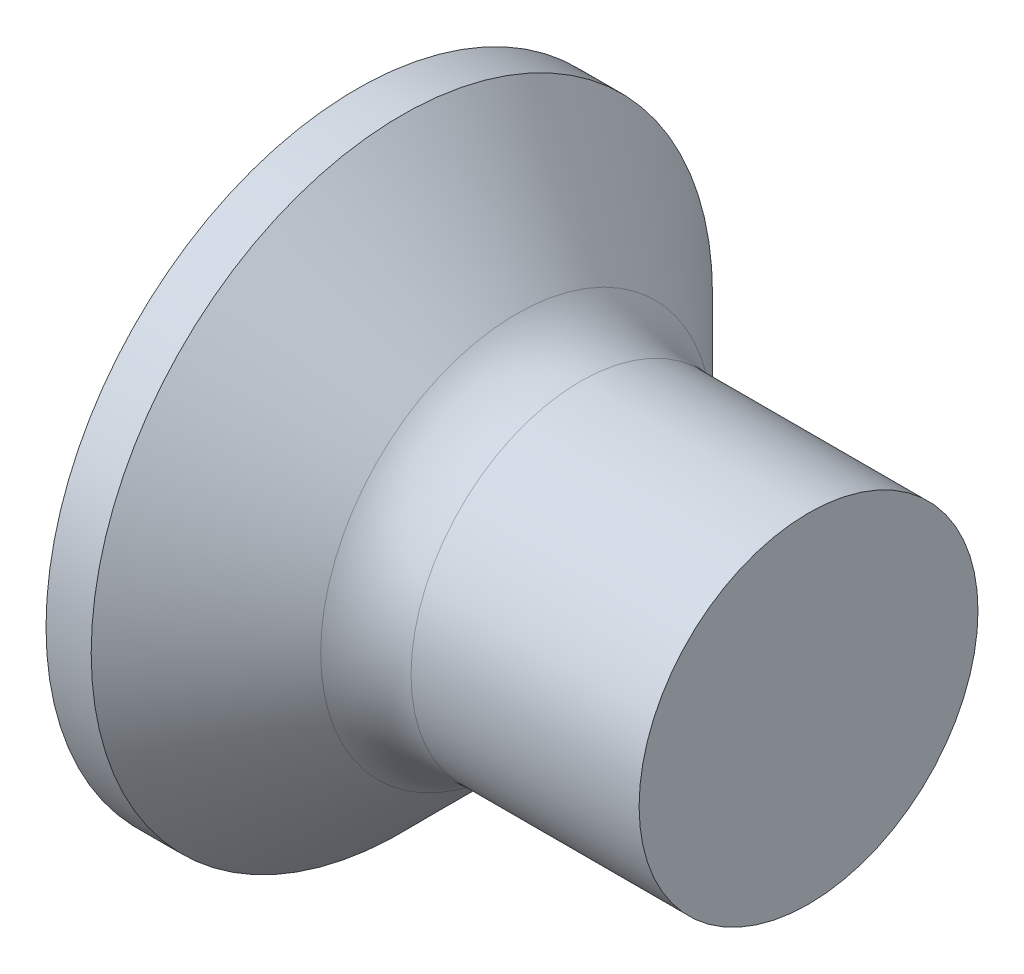
SolidWorks part; units mm, degrees
revolve "Base-Revolve" add sketch "BodySke"
sketch "BodySke" plane through (0, 0, 0) normal (0, 0, 1) x (1, 0, 0)
  line L0 (0, 0) -> (0, 2.75)
  line L1 (0, 2.75) -> (0.4, 2.75)
  line L2 (1.65, 1.5) -> (4, 1.5)
  line L3 (4, 1.5) -> (4, 0)
  line L4 (4, 0) -> (0, 0)
  line L5 (-6.35, 0) -> (82.55, 0) construction
  line L6 (1.65, -1.5) -> (4, -1.5) construction
  line L7 (0.4, -2.75) -> (1.65, -1.5) construction
  line L8 (0.4, 2.75) -> (1.65, 1.5)
  line L9 (0, -2.75) -> (0.4, -2.75) construction
  line L10 (2.15, 3.0875) -> (2.15, -6.4375) construction
  line L11 (0, 6.35) -> (0, -3.175) construction
  dimension "Diameter" = 3
  dimension "Length" = 4
  dimension "Head_ht" = 1.65
  dimension "Head_dia" = 5.5
  dimension "Head_ang" = 90
  dimension "D6" = 0.4
  dimension "Advance" = 0.5
  dimension "Thread_nom" = 4
cosmetic thread "ThreadCosmetic" [suppressed]
fillet "Fillet1" radius 0.8 1 edges at (1.65, 0, 1.5)
ref_plane "Plane1" through (0, 0, 0) normal (0, 0, 1) x (1, 0, 0)
ref_plane "Plane2" through (0, 0, 0) normal (0, 1, 0) x (1, 0, 0)
ref_plane "Plane3" through (0, 0, 0) normal (1, 0, 0) x (0, 0, -1)
sketch "Sketch3" plane through (0, 0, 0) normal (-1, 0, 0) x (0, 0, 1)
  line L0 (-0.37, 1.5) -> (0.37, 1.5)
  line L1 (0.37, 1.5) -> (0.37, -1.5)
  line L2 (0.37, -1.5) -> (-0.37, -1.5)
  line L3 (-0.37, -1.5) -> (-0.37, 1.5)
  dimension "Cross_dia" = 3
  dimension "Cross_width" = 0.74
  dimension "D1" = 1.5
  dimension "D2" = 0.37
ref_plane "Plane4" through (2.01, 0, 0) normal (-1, 0, 0) x (0, 0, 1)
sketch "Sketch4" plane through (2.01, 0, 0) normal (-1, 0, 0) x (0, 0, 1)
  line L0 (-0.37, 0.4979) -> (0.37, 0.4979)
  line L3 (0.37, 0.4979) -> (0.37, -0.4979)
  line L4 (0.37, -0.4979) -> (-0.37, -0.4979)
  line L5 (-0.37, -0.4979) -> (-0.37, 0.4979)
  dimension "D2" = 0.9957
  dimension "D1" = 0.74
  dimension "D4" = 0.4979
  dimension "D3" = 0.37
loft "Recess" cut profiles "Sketch3", "Sketch4"
pattern_circular "RecPat" count 2 every 90 about axis through (0, 0, 0) along (1, 0, 0) of "Recess"
sketch "RecCorSke" plane through (0, 0, 0) normal (0, 0, 1) x (1, 0, 0)
  line L0 (-3.175, 0) -> (15.875, 0) construction
  line L2 (0, 0) -> (0, 0.6966)
  line L3 (0, 0.6966) -> (2.01, 0.556)
  line L4 (2.01, 0.556) -> (2.1907, 0)
  line L5 (2.1907, 0) -> (0, 0)
  dimension "Diameter" = 1.112
  dimension "Depth" = 2.01
  dimension "Draft_angle" = 4
  dimension "Bottom_angle" = 18
revolve "RecessCore" cut sketch "RecCorSke" angle 360 about L0
sketch "ThdSchSke" plane through (0, 0, 0) normal (0, 0, 1) x (1, 0, 0)
  line L0 (2.15, -1.2195) -> (1.9536, -1.5)
  line L1 (2.15, -1.2195) -> (2.3464, -1.5)
  line L2 (2.3464, -1.5) -> (2.3464, -1.875)
  line L3 (-3.175, 0) -> (5.1513, 0) construction
  line L5 (2.3464, -1.875) -> (1.9536, -1.875)
  line L6 (1.9536, -1.875) -> (1.9536, -1.5)
  line L7 (0, 2.75) -> (0, -2.75) construction
  dimension "Diameter" = 3
  dimension "Thread_minor" = 2.439
  dimension "Start" = 2.15
revolve "ThreadSchematic" [suppressed] cut sketch "ThdSchSke" angle 360 about L3
pattern_linear "ThdSchPat" [suppressed]
equation "\"D1@Sketch3\" = \"Cross_dia@Sketch3\" / 2"
equation "\"D2@Sketch3\" = \"Cross_width@Sketch3\" / 2"
equation "\"Depth@RecCorSke\" = \"Cross_depth@Plane4\""
equation "\"D1@Sketch4\" = \"Cross_width@Sketch3\""
equation "\"D2@Sketch4\" = \"Cross_dia@Sketch3\" - 2.0 * \"Cross_depth@Plane4\" * tan(26.5  * 0.017453292)"
equation "\"D3@Sketch4\" = \"D1@Sketch4\" / 2"
equation "\"D4@Sketch4\" = \"D2@Sketch4\" / 2"
equation "\"Thread_length@ThreadCosmetic\" = ((sgn( (\"Length@BodySke\" - \"Advance@BodySke\" * 1.0 - \"Head_ht@BodySke\" ) - \"Thread_nom@BodySke\" )-1)*( (\"Length@BodySke\" - \"Advance@BodySke\" * 1.0 - \"Head_ht@BodySke\" ) - \"Thread_nom@BodySke\" ))/-2+ \"Thread_nom@BodySke\""
equation "\"Thread_minor@ThdSchSke\" = \"Thread_minor@ThreadCosmetic\""
equation "\"Diameter@ThdSchSke\" = \"Diameter@BodySke\""
equation "\"Overcut@ThdSchSke\" = \"Diameter@BodySke\" * 1.25"
equation "\"Start@ThdSchSke\" = 0.000001 + \"Length@BodySke\" - \"Thread_length@ThreadCosmetic\"  '---Countersunk---"
equation "\"Num_threads@ThdSchPat\" = int( \"Thread_length@ThreadCosmetic\" / \"Advance@BodySke\" + 0.999 )  + 1"
equation "\"Advance@ThdSchPat\" = \"Thread_length@ThreadCosmetic\" /  (\"Num_threads@ThdSchPat\" - 1) 'relax it"
